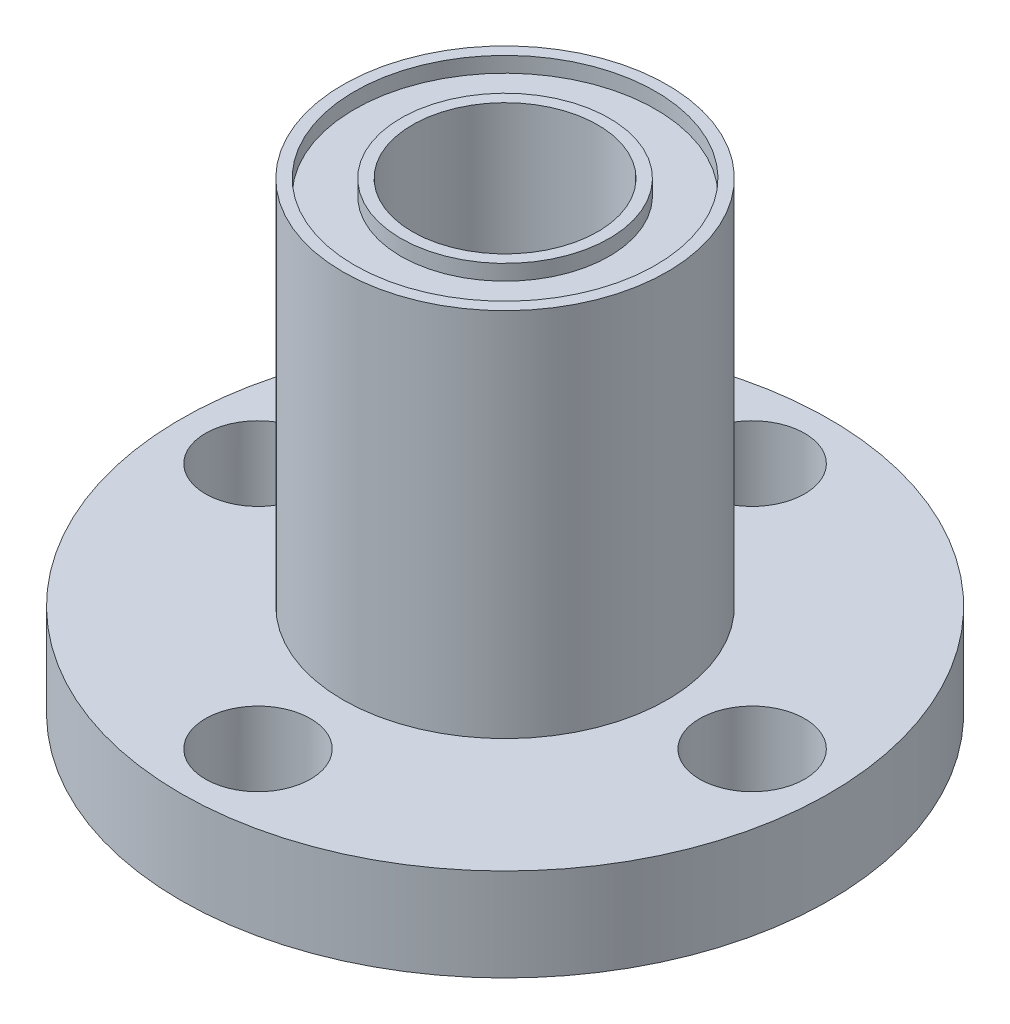
SolidWorks part; units mm, degrees
ref_plane "Front Plane" through (0, 0, 0) normal (0, 0, 1) x (1, 0, 0)
ref_plane "Top Plane" through (0, 0, 0) normal (0, 1, 0) x (1, 0, 0)
ref_plane "Right Plane" through (0, 0, 0) normal (1, 0, 0) x (0, 0, -1)
sketch "Sketch1" plane through (0, 0, 0) normal (0, 1, 0) x (1, 0, 0)
  circle A0 centre (0, 0) radius 21
  circle A1 centre (0, 0) radius 6
  dimension "D1" = 12
  dimension "D2" = 42
extrude "Boss-Extrude1" add sketch "Sketch1" along normal blind 6
sketch "Sketch2" plane through (0, 6, 0) normal (0, 1, 0) x (1, 0, 0)
  circle A0 centre (0, 0) radius 6
  circle A1 centre (0, 0) radius 10.5
  dimension "D1" = 21
  dimension "D2" = 12
extrude "Boss-Extrude2" add sketch "Sketch2" along normal blind 24
sketch "Sketch3" plane through (0, 30, 0) normal (0, 1, 0) x (1, 0, 0)
  circle A0 centre (0, 0) radius 6.75
  circle A1 centre (0, 0) radius 9.75
  dimension "D1" = 13.5
  dimension "D2" = 19.5
extrude "Cut-Extrude1" cut sketch "Sketch3" against normal blind 1
sketch "Sketch4" plane through (0, 6, 0) normal (0, 1, 0) x (1, 0, 0)
  line L0 (-34.9116, 0) -> (41.8314, 0) construction
  circle A0 centre (16, 0) radius 3.4
  point P5 (0, 0)
  dimension "D2" = 6.8
  dimension "D1" = 16
extrude "Cut-Extrude2" cut sketch "Sketch4" against normal through all both and the other way through all
pattern_circular "CirPattern1" count 4 over 360 about axis through (0, 0, 0) along (0, 1, 0) of "Cut-Extrude2"
